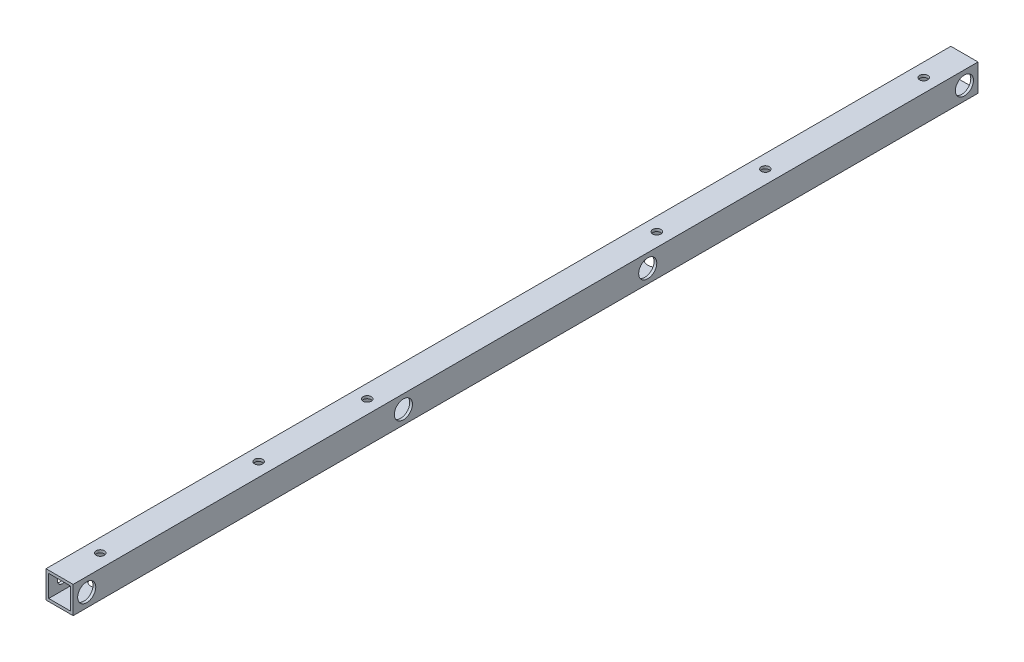
SolidWorks part; units mm, degrees
material "6063-T5"
ref_plane "正面" through (0, 0, 0) normal (0, 0, 1) x (1, 0, 0)
ref_plane "平面" through (0, 0, 0) normal (0, 1, 0) x (1, 0, 0)
ref_plane "右側面" through (0, 0, 0) normal (1, 0, 0) x (0, 0, -1)
sketch "ｽｹｯﾁ1" plane through (0, 0, 0) normal (0, 0, 1) x (1, 0, 0)
  line L1 (-7.5, -7.5) -> (7.5, -7.5)
  line L2 (-7.5, -7.5) -> (-7.5, 7.5)
  line L3 (-7.5, 7.5) -> (7.5, 7.5)
  line L4 (7.5, -7.5) -> (7.5, 7.5)
  line L5 (-7.5, -7.5) -> (7.5, 7.5) construction
  line L6 (-7.5, 7.5) -> (7.5, -7.5) construction
  line L7 (-6, -6) -> (6, -6)
  line L8 (-6, -6) -> (-6, 6)
  line L9 (-6, 6) -> (6, 6)
  line L10 (6, -6) -> (6, 6)
  line L11 (-6, -6) -> (6, 6) construction
  line L12 (-6, 6) -> (6, -6) construction
  point P0 (0, 0)
  point P6 (0, 0)
  dimension "D1" = 1.5
  dimension "D2" = 15
  dimension "D3" = 15
extrude "ﾎﾞｽ - 押し出し1" add sketch "ｽｹｯﾁ1" along normal blind 500
sketch "ｽｹｯﾁ2" plane through (7.5, 0, 0) normal (1, 0, 0) x (0, 0, -1)
  line L0 (-500, -7.5) -> (0, -7.5) construction
  line L1 (0, -7.5) -> (0, 7.5) construction
  line L2 (-500, -7.5) -> (-500, 7.5) construction
  line L3 (-500, 0) -> (0, 0) construction
  circle A4 centre (-492.5, 0) radius 2.7
  circle A8 centre (-7.5, 0) radius 2.7
  circle A9 centre (-317.5, 0) radius 2.7
  circle A10 centre (-182.5, 0) radius 2.7
  point P17 (-250, 0)
  dimension "D1" = 5.4
  dimension "D2" = 7.5
  dimension "D3" = 7.5
  dimension "D6" = 67.5
  dimension "D7" = 2
  dimension "D8" = 135
  dimension "D4" = 7.5
  dimension "D9" = 2
  dimension "D5" = 2
extrude "ｶｯﾄ - 押し出し1" cut sketch "ｽｹｯﾁ2" against normal blind 25
sketch "ｽｹｯﾁ3" plane through (0, 7.5, 0) normal (0, 1, 0) x (1, 0, 0)
  line L2 (7.5, -500) -> (7.5, 0) construction
  line L3 (7.5, 0) -> (-7.5, 0) construction
  circle A1 centre (0, -22.5) radius 2.25
  circle A6 centre (0, -477.5) radius 2.25
  dimension "D2" = 22.5
  dimension "D3" = 4.5
  dimension "D9" = 7.5
  dimension "D11" = 22.5
  dimension "D4" = 7.5
  dimension "D5" = 4.5
extrude "ｶｯﾄ - 押し出し2" cut sketch "ｽｹｯﾁ3" against normal blind 25
sketch "ｽｹｯﾁ4" plane through (0, -7.5, 0) normal (0, -1, 0) x (-1, 0, 0)
  line L0 (7.5, -500) -> (7.5, 0) construction
  line L1 (7.5, -500) -> (-7.5, -500) construction
  line L2 (7.5, 0) -> (-7.5, 0) construction
  circle A0 centre (0, -390) radius 2.25
  circle A1 centre (0, -330) radius 2.25
  circle A2 centre (0, -110) radius 2.25
  circle A3 centre (0, -170) radius 2.25
  dimension "D1" = 4.5
  dimension "D2" = 7.5
  dimension "D3" = 110
  dimension "D6" = 60
  dimension "D8" = 110
  dimension "D4" = 2
  dimension "D7" = 2
extrude "ｶｯﾄ - 押し出し3" cut sketch "ｽｹｯﾁ4" against normal blind 20
sketch "ｽｹｯﾁ5" plane through (0, -7.5, 0) normal (0, 1, 0) x (1, 0, 0)
  circle A0 centre (0, -22.5) radius 5
  circle A1 centre (0, -477.5) radius 5
  circle A2 centre (0, -390) radius 5
  circle A3 centre (0, -330) radius 5
  circle A4 centre (0, -110) radius 5
  circle A5 centre (0, -170) radius 5
  dimension "D1" = 10
  dimension "D2" = 10
  dimension "D3" = 10
  dimension "D4" = 10
  dimension "D5" = 10
  dimension "D6" = 10
extrude "ｶｯﾄ - 押し出し4" cut sketch "ｽｹｯﾁ5" along normal blind 10
sketch "ｽｹｯﾁ6" plane through (7.5, 0, 0) normal (1, 0, 0) x (0, 0, -1)
  circle A0 centre (-492.5, 0) radius 5
  circle A1 centre (-317.5, 0) radius 5
  circle A2 centre (-182.5, 0) radius 5
  circle A3 centre (-7.5, 0) radius 5
  dimension "D1" = 10
  dimension "D2" = 10
  dimension "D3" = 10
  dimension "D4" = 10
extrude "ｶｯﾄ - 押し出し5" cut sketch "ｽｹｯﾁ6" against normal blind 10
